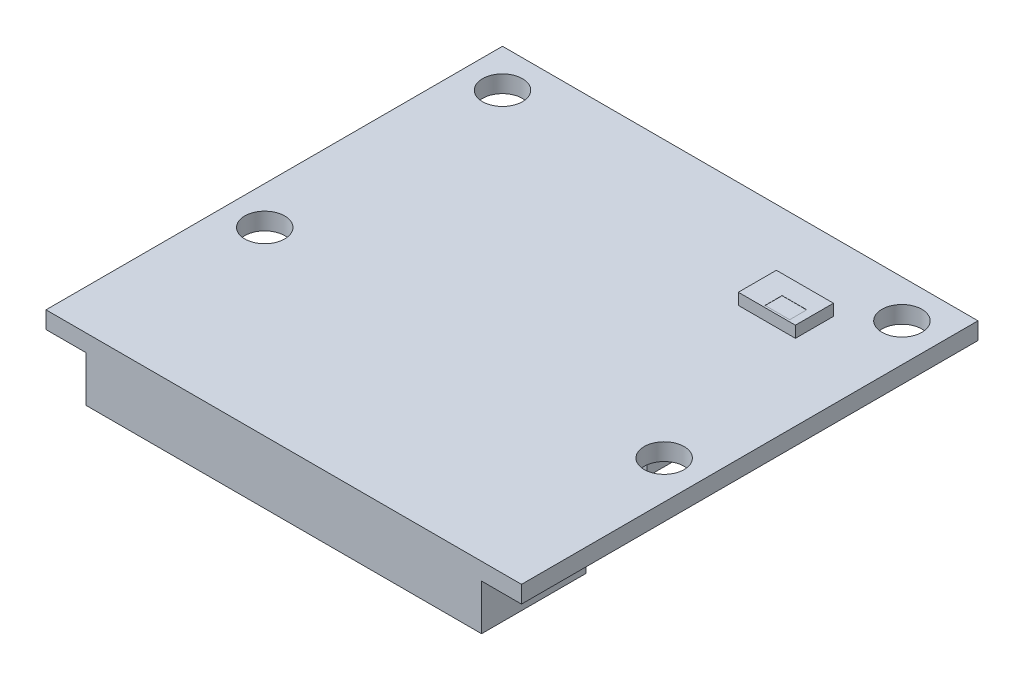
SolidWorks part; units mm, degrees
material "Epoxid, Ungefüllt"
ref_plane "Vorne" through (0, 0, 0) normal (0, 0, 1) x (1, 0, 0)
ref_plane "Oben" through (0, 0, 0) normal (0, 1, 0) x (1, 0, 0)
ref_plane "Rechts" through (0, 0, 0) normal (1, 0, 0) x (0, 0, -1)
sketch "Skizze1" plane through (0, 0, 0) normal (0, 1, 0) x (1, 0, 0)
  line L0 (0, 14.5) -> (0, -9.5) construction
  line L1 (-12.5, 14.5) -> (12.5, 14.5)
  line L2 (-12.5, 14.5) -> (-12.5, -9.5)
  line L3 (-12.5, -9.5) -> (12.5, -9.5)
  line L4 (12.5, 14.5) -> (12.5, -9.5)
  dimension "D1" = 24
  dimension "D2" = 25
  dimension "D3" = 9.5
extrude "PCB" add sketch "Skizze1" against normal blind 0.9
sketch "Skizze2" plane through (0, 0, 0) normal (0, 1, 0) x (1, 0, 0)
  line L0 (12.5, 14.5) -> (-12.5, 14.5) construction
  line L1 (12.5, -9.5) -> (12.5, 14.5) construction
  line L2 (0, 0) -> (0, 9.3158) construction
  circle A0 centre (10.5, 12.5) radius 1.05
  circle A1 centre (10.5, 0) radius 1.05
  circle A2 centre (-10.5, 0) radius 1.05
  circle A3 centre (-10.5, 12.5) radius 1.05
  dimension "D1" = 2.1
  dimension "D2" = 2
  dimension "D3" = 2
  dimension "D4" = 12.5
extrude "Mounting_Holes" cut sketch "Skizze2" against normal through all
sketch "Skizze3" plane through (0, -0.9, 0) normal (0, -1, 0) x (1, 0, 0)
  line L0 (0, 4) -> (0, 0) construction
  line L1 (-10.4, 9.5) -> (10.4, 9.5)
  line L2 (-10.4, 9.5) -> (-10.4, 4)
  line L3 (-10.4, 4) -> (10.4, 4)
  line L4 (10.4, 9.5) -> (10.4, 4)
  line L5 (-12.5, 9.5) -> (12.5, 9.5) construction
  dimension "D1" = 20.8
  dimension "D2" = 5.5
extrude "Connector_closed" add sketch "Skizze3" along normal blind 2.4
sketch "Skizze4" plane through (0, -0.9, 0) normal (0, -1, 0) x (1, 0, 0)
  line L0 (-12.5, -14.5) -> (-12.5, 9.5) construction
  line L1 (-9, -0.9) -> (8.7, -0.9)
  line L2 (-9, -0.9) -> (-9, -12.5)
  line L3 (-9, -12.5) -> (8.7, -12.5)
  line L4 (8.7, -0.9) -> (8.7, -12.5)
  line L5 (12.5, -14.5) -> (-12.5, -14.5) construction
  dimension "D1" = 17.7
  dimension "D2" = 3.5
  dimension "D3" = 2
  dimension "D4" = 13.6
extrude "Components_worst-case_Boundary-Box" add sketch "Skizze4" along normal blind 1.3
sketch "Skizze7" plane through (0, 0, 0) normal (0, 1, 0) x (1, 0, 0)
  line L0 (12.5, 14.5) -> (-12.5, 14.5) construction
  line L1 (5.5, 10.9) -> (8.5, 10.9)
  line L2 (5.5, 10.9) -> (5.5, 8.9)
  line L3 (5.5, 8.9) -> (8.5, 8.9)
  line L4 (8.5, 10.9) -> (8.5, 8.9)
  line L5 (12.5, -9.5) -> (12.5, 14.5) construction
  dimension "D1" = 5.6
  dimension "D2" = 3.6
  dimension "D3" = 4
  dimension "D4" = 7
extrude "Components_worst-case_Boundary-Box2" add sketch "Skizze7" along normal blind 0.6
sketch "Skizze8" plane through (0, 0.6, 0) normal (0, 1, 0) x (1, 0, 0)
  line L0 (12.5, -9.5) -> (12.5, 14.5) construction
  line L1 (8.1, 9) -> (6.8, 9)
  line L2 (8.1, 9) -> (8.1, 9.9)
  line L3 (8.1, 9.9) -> (6.8, 9.9)
  line L4 (6.8, 9) -> (6.8, 9.9)
  line L5 (12.5, 14.5) -> (-12.5, 14.5) construction
  dimension "D1" = 1.3
  dimension "D2" = 0.9
  dimension "D3" = 4.4
  dimension "D4" = 4.6
extrude "Status_LED" cut sketch "Skizze8" against normal blind 0.01
